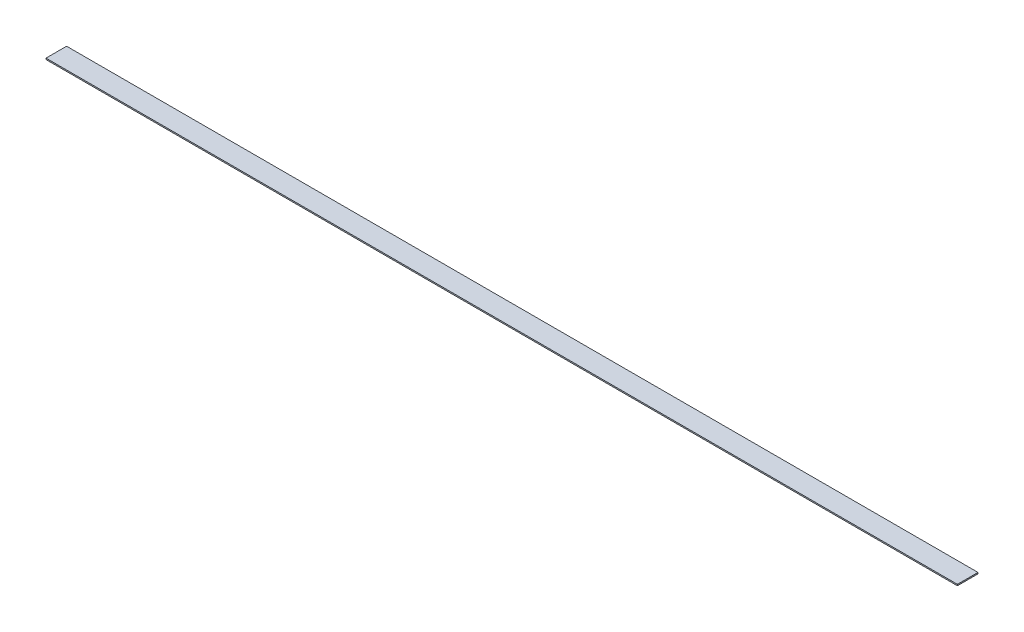
SolidWorks part; units mm, degrees
ref_plane "Front Plane" through (0, 0, 0) normal (0, 0, 1) x (1, 0, 0)
ref_plane "Top Plane" through (0, 0, 0) normal (0, 1, 0) x (1, 0, 0)
ref_plane "Right Plane" through (0, 0, 0) normal (1, 0, 0) x (0, 0, -1)
sketch "Sketch1" plane through (0, 0, 0) normal (0, 1, 0) x (1, 0, 0)
  line L1 (0, 0) -> (2247.9, 0)
  line L2 (0, 0) -> (0, 50.8)
  line L3 (0, 50.8) -> (2247.9, 50.8)
  line L4 (2247.9, 0) -> (2247.9, 50.8)
  dimension "D1" = 2247.9
  dimension "D2" = 50.8
extrude "Boss-Extrude1" add sketch "Sketch1" along normal blind 3.175
